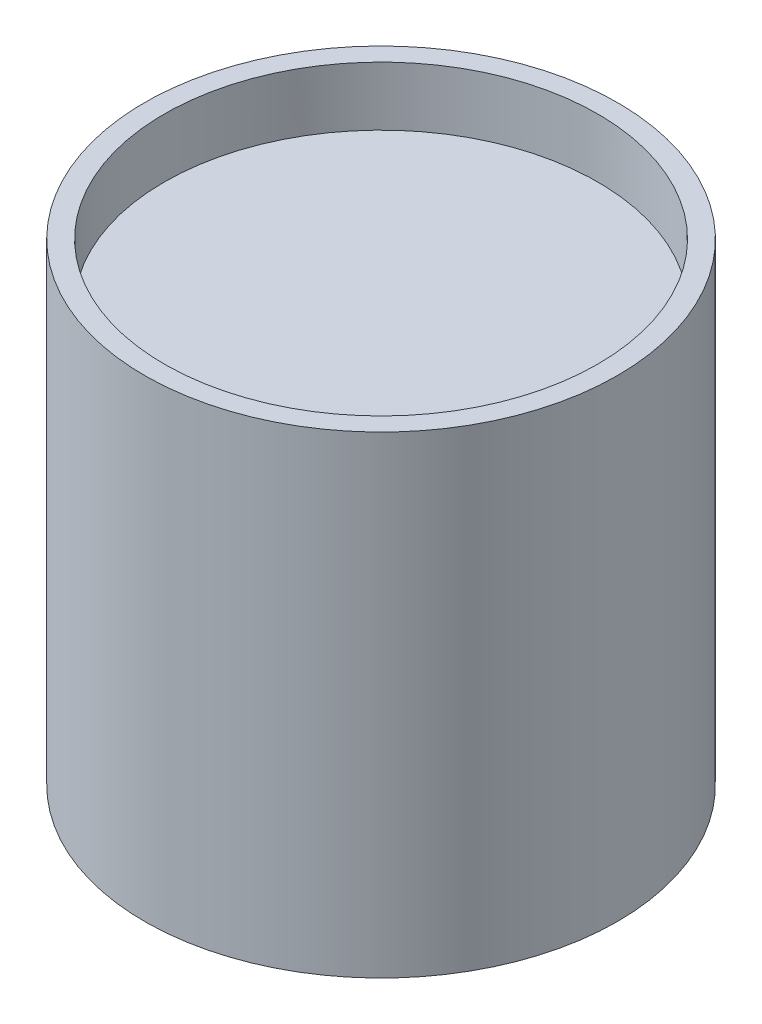
SolidWorks part; units mm, degrees
material "Glass"
ref_plane "Front Plane" through (0, 0, 0) normal (0, 0, 1) x (1, 0, 0)
ref_plane "Top Plane" through (0, 0, 0) normal (0, 1, 0) x (1, 0, 0)
ref_plane "Right Plane" through (0, 0, 0) normal (1, 0, 0) x (0, 0, -1)
sketch "Sketch1" plane through (0, 0, 0) normal (0, 0, 1) x (1, 0, 0)
  line L0 (0, -1000) -> (0, 49000) construction
  line L1 (34.925, 76.2) -> (34.925, 3.175)
  line L2 (34.925, 3.175) -> (0, 3.175)
  line L3 (0, 3.175) -> (0, 0)
  line L4 (0, 0) -> (38.1, 0)
  line L5 (38.1, 0) -> (38.1, 76.2)
  line L6 (38.1, 76.2) -> (34.925, 76.2)
  dimension "D1" = 76.2
  dimension "D2" = 76.2
  dimension "D3" = 3.175
  dimension "D4" = 3.175
revolve "Revolve1" add sketch "Sketch1" angle 360 about L0
sketch "Sketch2" plane through (0, 0, 0) normal (0, 0, 1) x (1, 0, 0)
  line L0 (0, 3.2004) -> (34.925, 3.2004)
  line L1 (34.925, 3.2004) -> (34.925, 66.7004)
  line L2 (34.925, 66.7004) -> (0, 66.7004)
  line L3 (0, 66.7004) -> (0, 3.2004)
  line L4 (-38.1, 0) -> (38.1, 0) construction
  line L5 (34.925, 3.175) -> (34.925, 76.2) construction
  dimension "D1" = 3.2004
  dimension "D3" = 63.5
revolve "Revolve2" add sketch "Sketch2" angle 360 about L3
